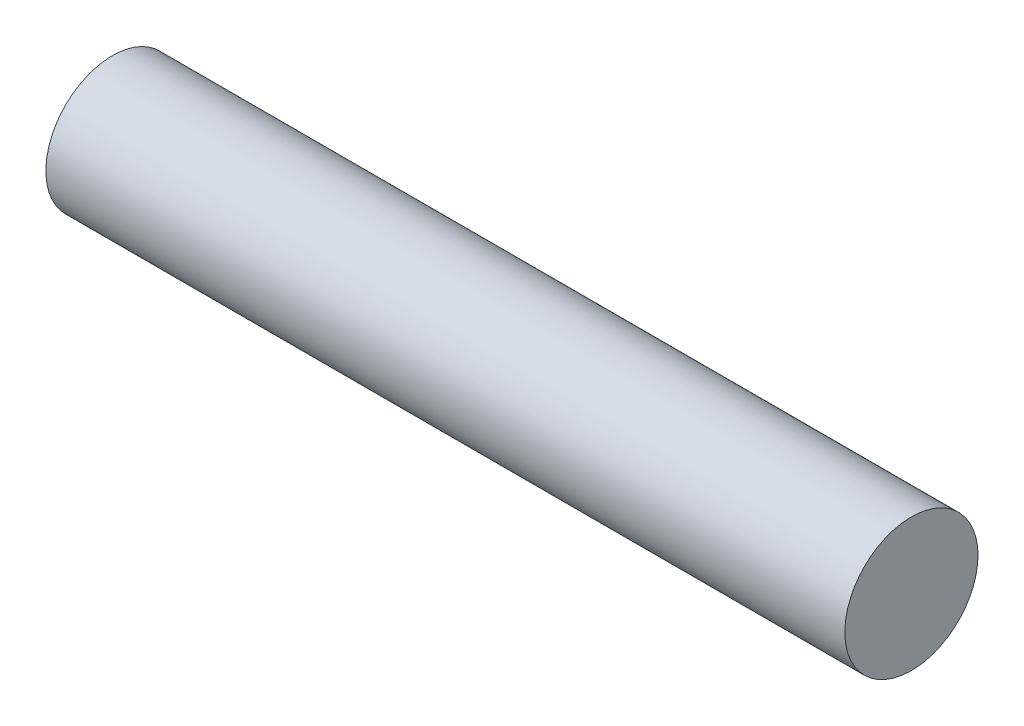
SolidWorks part; units mm, degrees
material "6061-T6 (SS)"
ref_plane "Front Plane" through (0, 0, 0) normal (0, 0, 1) x (1, 0, 0)
ref_plane "Top Plane" through (0, 0, 0) normal (0, 1, 0) x (1, 0, 0)
ref_plane "Right Plane" through (0, 0, 0) normal (1, 0, 0) x (0, 0, -1)
sketch "Sketch1" plane through (0, 0, 0) normal (1, 0, 0) x (0, 0, -1)
  circle A0 centre (0, 0) radius 6.35
  dimension "D1" = 12.7
extrude "Boss-Extrude1" add sketch "Sketch1" along normal blind 76.2
